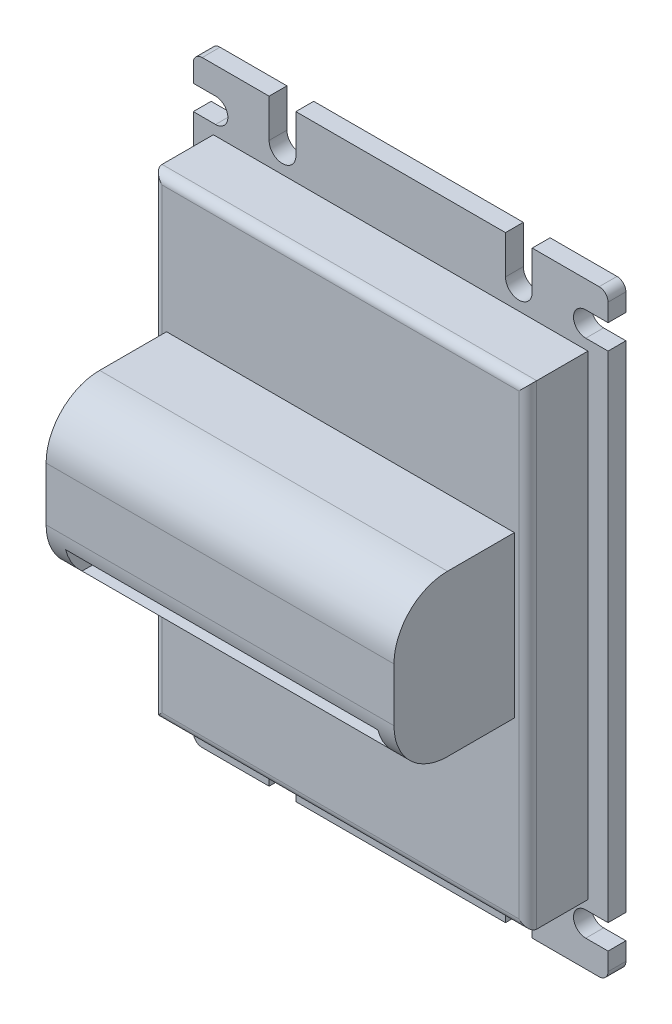
SolidWorks part; units mm, degrees
ref_plane "Front Plane" through (0, 0, 0) normal (0, 0, 1) x (1, 0, 0)
ref_plane "Top Plane" through (0, 0, 0) normal (0, 1, 0) x (1, 0, 0)
ref_plane "Right Plane" through (0, 0, 0) normal (1, 0, 0) x (0, 0, -1)
sketch "Sketch1" plane through (0, 0, 0) normal (0, 0, 1) x (1, 0, 0)
  line L1 (-46.5, 67) -> (46.5, 67)
  line L2 (-46.5, 67) -> (-46.5, -67)
  line L3 (-46.5, -67) -> (46.5, -67)
  line L4 (46.5, 67) -> (46.5, -67)
  line L5 (-46.5, 67) -> (46.5, -67) construction
  line L6 (-46.5, -67) -> (46.5, 67) construction
  point P0 (0, 0)
  dimension "D1" = 93
  dimension "D2" = 134
extrude "Boss-Extrude1" add sketch "Sketch1" along normal blind 4
sketch "Sketch2" plane through (0, 0, 4) normal (0, 0, 1) x (1, 0, 0)
  line L1 (-44, 53.25) -> (44, 53.25)
  line L2 (-44, 53.25) -> (-44, -53.25)
  line L3 (-44, -53.25) -> (44, -53.25)
  line L4 (44, 53.25) -> (44, -53.25)
  line L5 (-44, 53.25) -> (44, -53.25) construction
  line L6 (-44, -53.25) -> (44, 53.25) construction
  point P0 (0, 0)
  dimension "D1" = 88
  dimension "D2" = 106.5
extrude "Boss-Extrude2" add sketch "Sketch2" along normal blind 13.5
fillet "Fillet2" radius 2 4 edges at (46.5, -67, 2) (-46.5, -67, 2) (-46.5, 67, 2) (46.5, 67, 2)
sketch "Sketch5" plane through (0, 0, 17.5) normal (0, 0, 1) x (1, 0, 0)
  line L10 (-39, 23.25) -> (-39, -12.75)
  line L11 (-39, 23.25) -> (39, 23.25)
  line L12 (-39, -12.75) -> (39, -12.75)
  line L13 (39, 23.25) -> (39, -12.75)
  point P0 (-15.0531, 5.25)
extrude "Boss-Extrude3" add sketch "Sketch5" along normal blind 27
fillet "Fillet3" radius 12 2 edges at (0, -12.75, 44.5) (0, 23.25, 44.5)
sketch "Sketch6" plane through (0, 0, 44.5) normal (0, 0, 1) x (1, 0, 0)
  line L0 (-39, -12.75) -> (39, -12.75) construction
  line L1 (-35, -3.75) -> (35, -3.75)
  line L2 (-35, -3.75) -> (-35, -9.75)
  line L3 (-35, -9.75) -> (35, -9.75)
  line L4 (35, -3.75) -> (35, -9.75)
  line L5 (39, -12.75) -> (39, -0.75) construction
  line L6 (-39, 23.25) -> (-39, -12.75) construction
  dimension "D1" = 3
  dimension "D2" = 4
  dimension "D3" = 4
  dimension "D4" = 6
extrude "Cut-Extrude1" cut sketch "Sketch6" against normal through all
sketch "Sketch8" plane through (0, 0, 4) normal (0, 0, 1) x (1, 0, 0)
  line L0 (44.5, 67) -> (-44.5, 67) construction
  line L1 (23.5, 67) -> (29.5, 67)
  line L2 (23.5, 67) -> (23.5, 58.4)
  line L3 (23.5, 58.4) -> (29.5, 58.4)
  line L4 (29.5, 67) -> (29.5, 58.4)
  line L5 (46.5, -65) -> (46.5, 65) construction
  line L6 (0, 67) -> (0, 53.25)
  line L7 (44, 53.25) -> (-44, 53.25) construction
  line L8 (46.5, 0) -> (44, 0)
  line L9 (44, -53.25) -> (44, 53.25) construction
  line L10 (-23.5, 58.4) -> (-29.5, 58.4)
  line L11 (-29.5, 67) -> (-29.5, 58.4)
  line L12 (-23.5, 67) -> (-29.5, 67)
  line L13 (-23.5, 67) -> (-23.5, 58.4)
  line L14 (-23.5, -67) -> (-23.5, -58.4)
  line L15 (-23.5, -67) -> (-29.5, -67)
  line L16 (-29.5, -67) -> (-29.5, -58.4)
  line L17 (-23.5, -58.4) -> (-29.5, -58.4)
  line L18 (23.5, -58.4) -> (29.5, -58.4)
  line L19 (29.5, -67) -> (29.5, -58.4)
  line L20 (23.5, -67) -> (29.5, -67)
  line L21 (23.5, -67) -> (23.5, -58.4)
  circle A0 centre (26.5, 58.4) radius 3
  circle A1 centre (-26.5, 58.4) radius 3
  circle A2 centre (-26.5, -58.4) radius 3
  circle A3 centre (26.5, -58.4) radius 3
  line M17 (-44.5, -67) -> (44.5, -67)
  line M21 (44.5, 67) -> (-44.5, 67)
  dimension "D1" = 6
  dimension "D2" = 23
  dimension "D3" = 8.6
sketch "Sketch9" plane through (0, 0, 4) normal (0, 0, 1) x (1, 0, 0)
  line L0 (46.5, -65) -> (46.5, 65) construction
  line L1 (46.5, 61) -> (41.5, 61)
  line L2 (46.5, 61) -> (46.5, 55.5)
  line L3 (46.5, 55.5) -> (41.5, 55.5)
  line L4 (41.5, 61) -> (41.5, 55.5)
  line L5 (44.5, 67) -> (32.5, 67) construction
  line L6 (0, 67) -> (0, 55.5)
  line L7 (23.5, 67) -> (-23.5, 67) construction
  line L8 (46.5, 0) -> (44, 0)
  line L9 (44, -53.25) -> (44, 53.25) construction
  line L10 (-41.5, 61) -> (-41.5, 55.5)
  line L11 (-46.5, 61) -> (-41.5, 61)
  line L12 (-46.5, 55.5) -> (-41.5, 55.5)
  line L13 (-46.5, -61) -> (-41.5, -61)
  line L14 (-46.5, -55.5) -> (-41.5, -55.5)
  line L15 (46.5, -55.5) -> (41.5, -55.5)
  line L16 (41.5, -61) -> (41.5, -55.5)
  line L17 (46.5, -61) -> (41.5, -61)
  line L18 (46.5, -61) -> (46.5, -55.5)
  line L19 (-46.5, 55.5) -> (-46.5, 61)
  line L20 (-46.5, -61) -> (-46.5, -55.5)
  line L21 (-41.5, -55.5) -> (-41.5, -61)
  circle A0 centre (41.5, 58.25) radius 2.75
  circle A1 centre (-41.5, 58.25) radius 2.75
  circle A2 centre (-41.5, -58.25) radius 2.75
  circle A3 centre (41.5, -58.25) radius 2.75
  line M28 (-46.5, 65) -> (-46.5, -65)
  dimension "D1" = 5
  dimension "D2" = 5.5
  dimension "D3" = 6
extrude "Cut-Extrude3" cut sketch "Sketch9" against normal blind 10 contours A1 L10 | A1 L10 | L12 A1 L11 M28 | A2 L14 L13 M28 | A0 | L2 L3 L4 L1 | A3 | L18 L15 L16 L17
extrude "Cut-Extrude6" cut sketch "Sketch8" against normal blind 10 contours L19 A3 L21 M17 | A3 L18 | A3 L18 | L17 A2 | L17 A2 | A0 L4 L2 M21 | L3 A0 | L3 A0 | L11 A1 L13 M21 | A1 L10 | A1 L10
sketch "Sketch13" plane through (0, 0, 17.5) normal (0, 0, 1) x (1, 0, 0)
  line L0 (-44, -53.25) -> (44, -53.25) construction
  line L1 (-44, 53.25) -> (-42, 53.25)
  line L2 (-44, 53.25) -> (-44, -53.25)
  line L3 (-44, -53.25) -> (-42, -53.25)
  line L4 (-42, 53.25) -> (-42, -53.25)
  line L5 (0, 53.25) -> (0, 38.2709)
  line L6 (44, 53.25) -> (-44, 53.25) construction
  line L7 (44, -53.25) -> (42, -53.25)
  line L8 (42, 53.25) -> (42, -53.25)
  line L9 (44, 53.25) -> (42, 53.25)
  line L10 (44, 53.25) -> (44, -53.25)
  dimension "D1" = 2
extrude "Cut-Extrude7" cut sketch "Sketch13" against normal up to surface (13.5 mm away) contours L2 L1 L4 L3 | L7 L8 L9 L10 up to face at (0, 0, 4)
fillet "Fillet4" radius 2 4 edges at (0, -53.25, 17.5) (42, 0, 17.5) (-42, 0, 17.5) (0, 53.25, 17.5)
